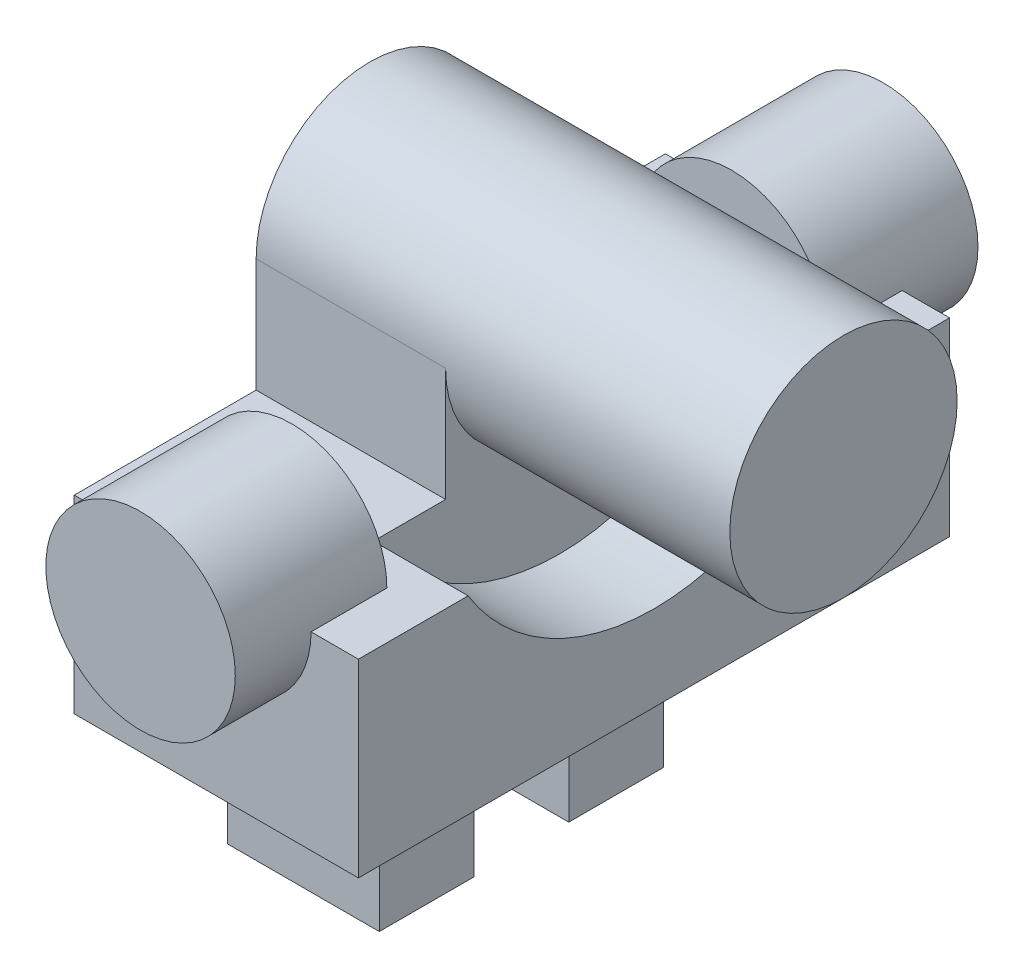
SolidWorks part; units mm, degrees
ref_plane "Alzado" through (0, 0, 0) normal (0, 0, 1) x (1, 0, 0)
ref_plane "Planta" through (0, 0, 0) normal (0, 1, 0) x (1, 0, 0)
ref_plane "Vista lateral" through (0, 0, 0) normal (1, 0, 0) x (0, 0, -1)
sketch "Croquis2" plane through (0, 0, 0) normal (1, 0, 0) x (0, 0, -1)
  circle A0 centre (0, 0) radius 6
  dimension "D1" = 12
extrude "Saliente-Extruir1" add sketch "Croquis2" along normal mid plane 25
sketch "Croquis3" plane through (-12.5, 0, 0) normal (-1, 0, 0) x (0, 0, 1)
  line L0 (-15.6, -6) -> (-6, -6)
  line L2 (-15.6, -6) -> (-15.6, -16)
  line L3 (-15.6, -16) -> (15.6, -16)
  line L4 (15.6, -6) -> (15.6, -16)
  line L5 (6, 0) -> (6, -6)
  line L6 (6, 0) -> (-6, 0)
  line L7 (-6, 0) -> (-6, -6)
  line L8 (6, -6) -> (15.6, -6)
  line L9 (0, 0) -> (0, -12.4243) construction
  circle A0 centre (0, 0) radius 6 construction
  point P0 (0, 0)
  point P15 (0, -16)
  dimension "D1" = 31.2
  dimension "D2" = 10
  dimension "D3" = 6
extrude "Saliente-Extruir2" add sketch "Croquis3" against normal blind 15
sketch "Croquis5" plane through (2.5, 0, 0) normal (1, 0, 0) x (0, 0, -1)
  circle A0 centre (0, 0) radius 11.5
  circle A1 centre (0, 0) radius 6
  dimension "D1" = 23
extrude "Cortar-Extruir2" cut sketch "Croquis5" against normal blind 5
sketch "Croquis6" plane through (-12.5, 0, 0) normal (-1, 0, 0) x (0, 0, 1)
  line L0 (0, 0) -> (0, -21.4751) construction
  line L1 (-15.6, -16) -> (15.6, -16) construction
  line L2 (7.5, -16) -> (2.5, -16)
  line L3 (7.5, -16) -> (7.5, -26)
  line L4 (7.5, -26) -> (2.5, -26)
  line L5 (2.5, -16) -> (2.5, -26)
  line L6 (-7.5, -26) -> (-2.5, -26)
  line L7 (-2.5, -16) -> (-2.5, -26)
  line L8 (-7.5, -16) -> (-2.5, -16)
  line L9 (-7.5, -16) -> (-7.5, -26)
  point P9 (2.5, -21)
  dimension "D1" = 5
  dimension "D2" = 10
  dimension "D3" = 5
extrude "Saliente-Extruir3" add sketch "Croquis6" against normal blind 8
sketch "Croquis7" plane through (0, 0, 7.5) normal (0, 0, 1) x (1, 0, 0)
  line L0 (-4.5, -26) -> (-12.5, -26) construction
  circle A0 centre (-8.5, -22.3) radius 1.7
  dimension "D1" = 3.4
  dimension "D2" = 3.7
extrude "Cortar-Extruir3" cut sketch "Croquis7" against normal up to surface (15 mm away) up to face at (-8.5, -21, -7.5)
sketch "Croquis8" plane through (0, 0, 15.6) normal (0, 0, 1) x (1, 0, 0)
  line L0 (2.5, -6) -> (-12.5, -6) construction
  circle A0 centre (-5, -6) radius 5
  dimension "D1" = 10
extrude "Saliente-Extruir4" add sketch "Croquis8" along normal mid plane 8
mirror "Simetría1" about plane through (0, 0, 0) normal (0, 0, 1) of "Saliente-Extruir4"
